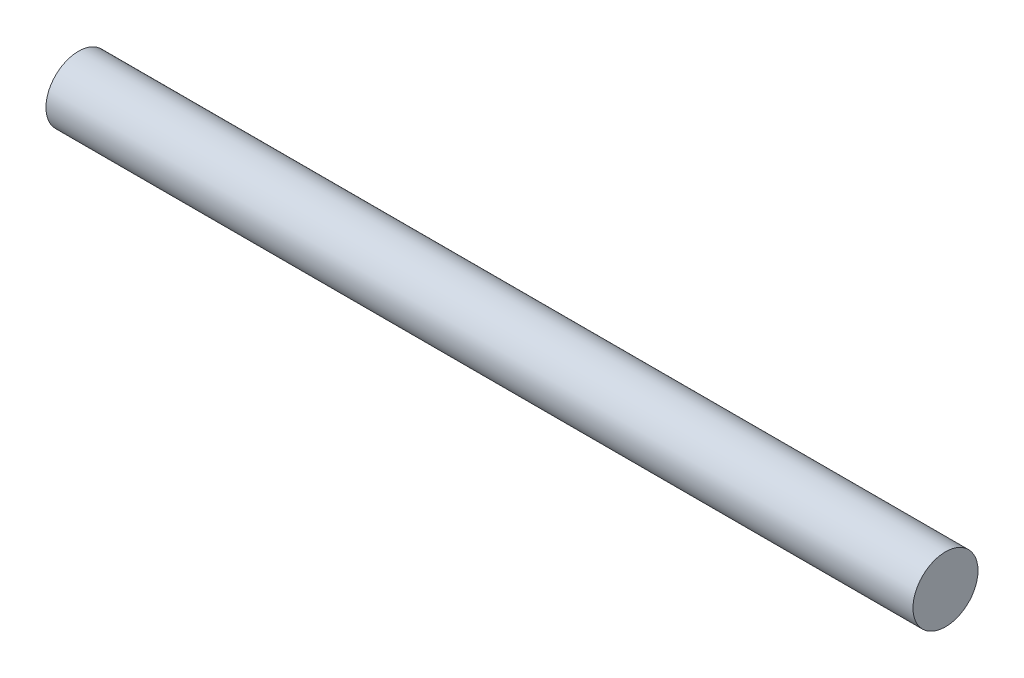
SolidWorks part; units mm, degrees
ref_plane "Front Plane" through (0, 0, 0) normal (0, 0, 1) x (1, 0, 0)
ref_plane "Top Plane" through (0, 0, 0) normal (0, 1, 0) x (1, 0, 0)
ref_plane "Right Plane" through (0, 0, 0) normal (1, 0, 0) x (0, 0, -1)
sketch "Sketch1" plane through (0, 0, 0) normal (1, 0, 0) x (0, 0, -1)
  circle A0 centre (0, 0) radius 0.375
  dimension "D1" = 0.75
extrude "Boss-Extrude1" add sketch "Sketch1" along normal mid plane 10
